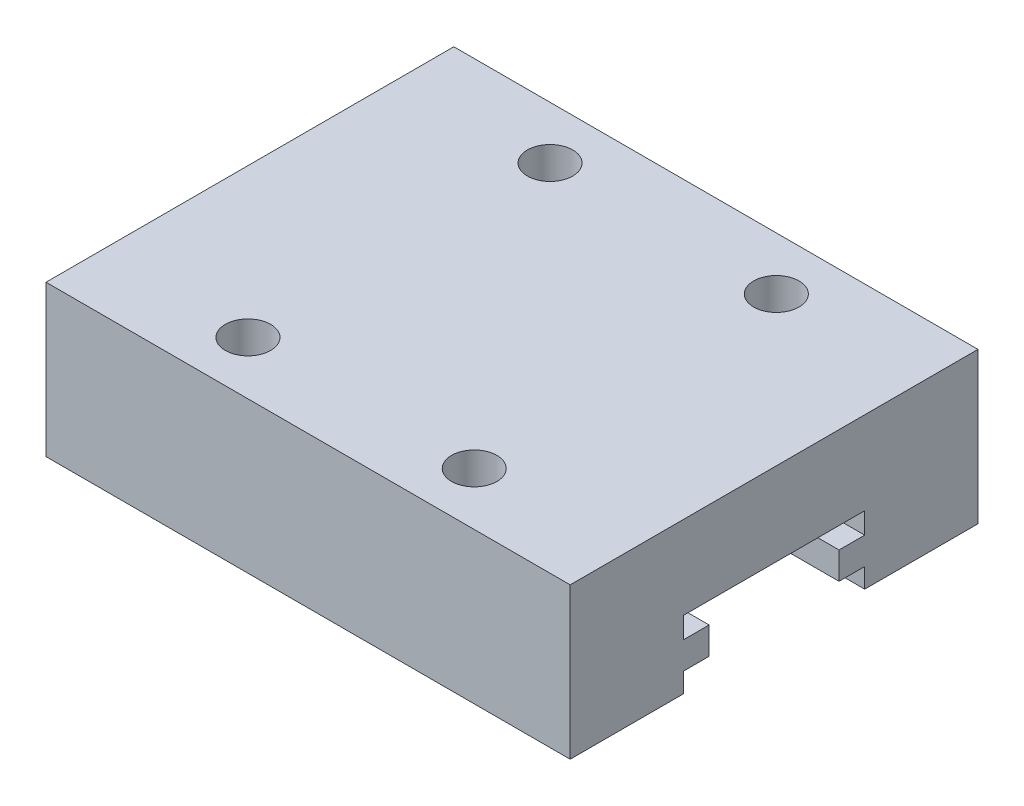
SolidWorks part; units mm, degrees
ref_plane "Alzado" through (0, 0, 0) normal (0, 0, 1) x (1, 0, 0)
ref_plane "Planta" through (0, 0, 0) normal (0, 1, 0) x (1, 0, 0)
ref_plane "Vista lateral" through (0, 0, 0) normal (1, 0, 0) x (0, 0, -1)
sketch "Croquis1" plane through (0, 0, 0) normal (0, 1, 0) x (1, 0, 0)
  line L2 (0, 0) -> (34.7, 0)
  line L3 (0, 0) -> (0, 27)
  line L4 (0, 27) -> (34.7, 27)
  line L5 (34.7, 0) -> (34.7, 27)
  dimension "D1" = 34.7
  dimension "D2" = 27
extrude "Saliente-Extruir1" add sketch "Croquis1" along normal blind 10
sketch "Croquis2" plane through (0, 10, 0) normal (0, 1, 0) x (1, 0, 0)
  line L0 (0, 0) -> (34.7, 0) construction
  line L2 (17.35, 0) -> (17.35, 27) construction
  line L3 (34.7, 27) -> (0, 27) construction
  circle A0 centre (9.85, 23.5201) radius 1.5
  circle A1 centre (24.85, 23.5) radius 1.5
  circle A2 centre (9.85, 3.5201) radius 1.5
  circle A3 centre (24.85, 3.5) radius 1.5
  point P14 (23.9525, 3.5201)
  point P15 (0, 0)
  point P16 (8.9972, 3.5)
  dimension "D1" = 3
  dimension "D2" = 15
  dimension "D3" = 15
  dimension "D4" = 20
  dimension "D5" = 20
  dimension "D6" = 3.5
  dimension "D7" = 7.5
  dimension "D8" = 15
  dimension "D9" = 7.5
extrude "Cortar-Extruir1" cut sketch "Croquis2" against normal blind 5
sketch "Croquis3" plane through (34.7, 0, 0) normal (1, 0, 0) x (0, 0, -1)
  line L0 (0, 0) -> (27, 0) construction
  line L1 (7.5, 0) -> (19.5, 0)
  line L2 (7.5, 0) -> (7.5, 1.3)
  line L3 (7.5, 4.5) -> (19.5, 4.5)
  line L4 (19.5, 0) -> (19.5, 1.3)
  line L5 (13.5, 10) -> (13.5, 0) construction
  line L6 (0, 10) -> (27, 10) construction
  line L7 (7.5, 3.1) -> (7.5, 4.5)
  line L8 (7.5, 3.1) -> (9.2, 3.1)
  line L10 (7.5, 1.3) -> (9.2, 1.3)
  line L11 (9.2, 3.1) -> (9.2, 1.3)
  line L12 (19.5, 1.3) -> (17.8, 1.3)
  line L13 (19.5, 3.1) -> (17.8, 3.1)
  line L14 (17.8, 3.1) -> (17.8, 1.3)
  line L15 (19.5, 3.1) -> (19.5, 4.5)
  dimension "D2" = 4.5
  dimension "D3" = 6
  dimension "D4" = 1.8
  dimension "D5" = 1.7
  dimension "D6" = 1.4
extrude "Cortar-Extruir2" cut sketch "Croquis3" against normal up to surface (34.7 mm away) up to face at (0, 5, -13.5)
